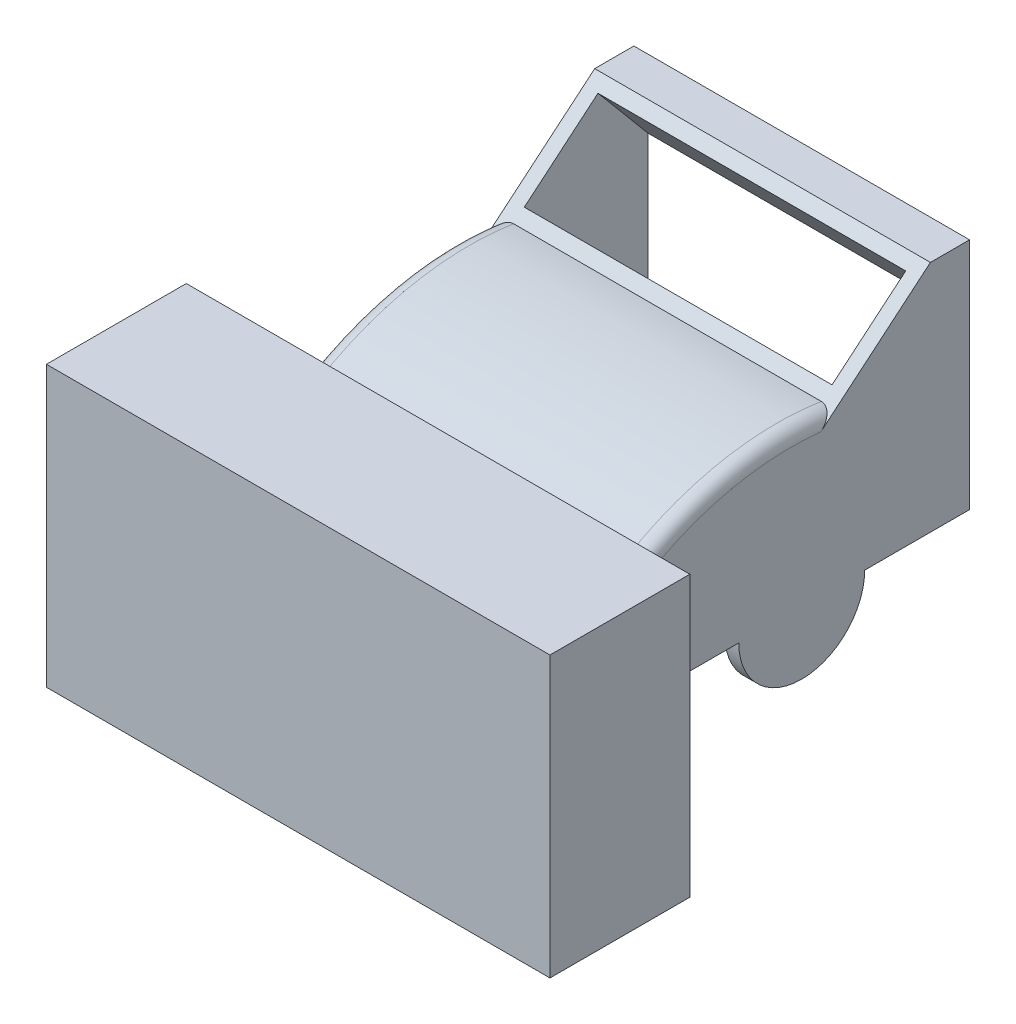
SolidWorks part; units mm, degrees
ref_plane "Ön Düzlem" through (0, 0, 0) normal (0, 0, 1) x (1, 0, 0)
ref_plane "Üst Düzlem" through (0, 0, 0) normal (0, 1, 0) x (1, 0, 0)
ref_plane "Sağ Düzlem" through (0, 0, 0) normal (1, 0, 0) x (0, 0, -1)
sketch "Çizim1" plane through (0, 0, 0) normal (0, 0, 1) x (1, 0, 0)
  line L0 (0, -80.5014) -> (0, 80.5014) construction
  line L1 (-134.08, 0) -> (134.08, 0) construction
  line L2 (-60, 0) -> (-60, 30)
  line L3 (-60, 30) -> (60, 30)
  line L4 (60, 30) -> (60, -20)
  line L5 (60, -20) -> (-60, -20)
  line L6 (-60, -20) -> (-60, 0)
  line L7 (-60, 30) -> (-60, 75)
  line L8 (-60, 75) -> (60, 75)
  line L9 (60, 75) -> (60, 30)
  point P4 (0, 0)
  point P8 (0, 0)
  dimension "D1" = 120
  dimension "D2" = 60
  dimension "D3" = 20
  dimension "D4" = 30
  dimension "D5" = 45
extrude "Yükseklik-Ekstrüzyon1" add sketch "Çizim1" against normal blind 120 contours L9 L8 L7 L3 | L6 L5 L4 L3 L2
sketch "Çizim2" plane through (60, 0, 0) normal (1, 0, 0) x (0, 0, -1)
  line L0 (0, -20) -> (0, 20)
  line L1 (0, 75) -> (0, -20) construction
  line L2 (72, 35) -> (106, 63.5294)
  line L3 (106, 63.5294) -> (120, 63.5294)
  line L4 (120, 75) -> (120, -20) construction
  line L6 (72, 35) -> (104.5102, 35) construction
  line L7 (120, -20) -> (0, -20) construction
  line L8 (120, 75) -> (120, -20)
  line L9 (120, -20) -> (0, -20)
  arc A0 (0, 20) -> (72, 35) centre (56.0589, -68.7829) cw
  line M5 (0, 75) -> (0, -20)
  line M7 (120, -20) -> (120, 75)
  line M8 (120, 75) -> (0, 75)
  dimension "D1" = 40
  dimension "D3" = 105
  dimension "D2" = 35
  dimension "D4" = 72
  dimension "D5" = 40
  dimension "D6" = 14
extrude "Kes-Ekstrüzyon1" cut sketch "Çizim2" against normal blind 120 contours A0 L2 L3 M5 M7 M8
sketch "Çizim3" plane through (0, -14.9142, -12.5145) normal (0, 0.766, 0.6428) x (1, 0, 0)
  line L0 (-60, 77.6528) -> (-60, 122.0366) construction
  line L1 (-55, 117.0366) -> (55, 117.0366)
  line L2 (-55, 117.0366) -> (-55, 82.6528)
  line L3 (-55, 82.6528) -> (55, 82.6528)
  line L4 (55, 117.0366) -> (55, 82.6528)
  line L5 (60, 77.6528) -> (60, 122.0366) construction
  line L6 (-60, 122.0366) -> (60, 122.0366) construction
  line L7 (-60, 77.6528) -> (60, 77.6528) construction
  dimension "D1" = 5
  dimension "D2" = 5
  dimension "D3" = 5
  dimension "D4" = 5
extrude "Kes-Ekstrüzyon2" cut sketch "Çizim3" against normal blind 120
sketch "Çizim4" plane through (0, 0, 0) normal (1, 0, 0) x (0, 0, -1)
  line L0 (0, 20) -> (0, -20) construction
  line L1 (6, 15.5294) -> (115, 15.5294)
  line L2 (6, 15.5294) -> (6, -15)
  line L3 (6, -15) -> (115, -15)
  line L4 (115, 15.5294) -> (115, -15)
  line L5 (120, 63.5294) -> (120, -20) construction
  line L6 (120, -20) -> (0, -20) construction
  line L7 (106, 63.5294) -> (120, 63.5294) construction
  dimension "D1" = 6
  dimension "D2" = 5
  dimension "D3" = 5
  dimension "D4" = 48
extrude "Kes-Ekstrüzyon3" cut sketch "Çizim4" against normal blind 55 and the other way blind 55
ref_plane "Düzlem1" through (0, 0, -120) normal (0, 0, 1) x (1, 0, 0)
sketch "Çizim5" plane through (0, 0, -120) normal (0, 0, 1) x (1, 0, 0)
  line L9 (60, 63.5294) -> (60, -20) construction
  line L10 (47, 30.2139) -> (-47, 30.2139)
  line L11 (47, 30.2139) -> (47, -8)
  line L12 (47, -8) -> (-47, -8)
  line L13 (-47, 30.2139) -> (-47, -8)
  line L14 (-60, -20) -> (-60, 63.5294) construction
  line L15 (60, -20) -> (-60, -20) construction
  line L16 (-55, 38.2139) -> (55, 38.2139) construction
  dimension "D1" = 13
  dimension "D2" = 13
  dimension "D3" = 12
  dimension "D4" = 8
extrude "Kes-Ekstrüzyon4" cut sketch "Çizim5" along normal blind 95
sketch "Çizim6" plane through (60, 0, 0) normal (1, 0, 0) x (0, 0, -1)
  line L0 (120, -20) -> (0, -20) construction
  circle A0 centre (60, -20) radius 22.5
  dimension "D1" = 45
extrude "Yükseklik-Ekstrüzyon2" add sketch "Çizim6" against normal blind 5
sketch "Çizim7" plane through (-60, 0, 0) normal (-1, 0, 0) x (0, 0, 1)
  line L0 (-37.5, -20) -> (-82.5, -20) construction
  circle A0 centre (-60, -20) radius 22.5
  dimension "D1" = 45
extrude "Yükseklik-Ekstrüzyon3" add sketch "Çizim7" along normal blind 5
fillet "Radyus1" radius 5 5 edges at (-60, 34.0101, -34.6437) (60, 34.0101, -34.6437) (60, 0, 0) (0, 20, 0) (-60, 0, 0)
sketch "Çizim8" plane through (0, 0, 0) normal (1, 0, 0) x (0, 0, -1)
  line L1 (-10, -60) -> (-60, -60)
  line L2 (-10, -60) -> (-10, 40)
  line L3 (-10, 40) -> (-60, 40)
  line L4 (-60, -60) -> (-60, 40)
  point P4 (-10, -55.3117)
  dimension "D1" = 10
  dimension "D2" = 50
  dimension "D3" = 50
  dimension "D4" = 40
  dimension "D5" = 50
  dimension "D6" = 60
extrude "Yükseklik-Ekstrüzyon4" add sketch "Çizim8" against normal blind 90 and the other way blind 90 separate body
